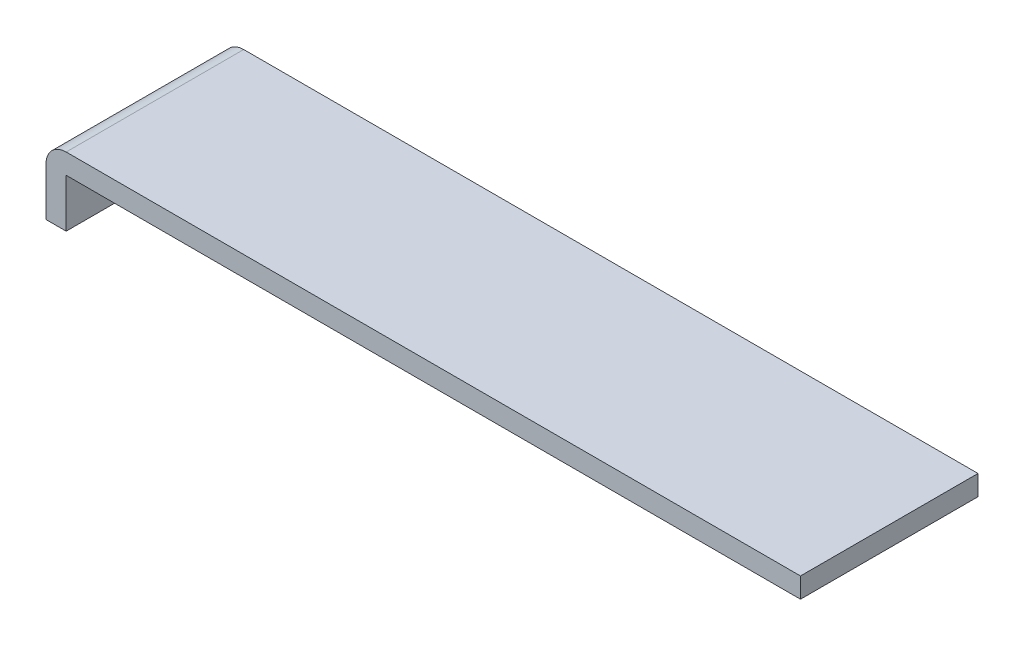
SolidWorks part; units mm, degrees
ref_plane "Plan de face" through (0, 0, 0) normal (0, 0, 1) x (1, 0, 0)
ref_plane "Plan de dessus" through (0, 0, 0) normal (0, 1, 0) x (1, 0, 0)
ref_plane "Plan de droite" through (0, 0, 0) normal (1, 0, 0) x (0, 0, -1)
sketch "Esquisse1" plane through (0, 0, 0) normal (0, 0, 1) x (1, 0, 0)
  line L0 (0, 0) -> (0, 1.7)
  line L1 (0, 1.7) -> (18.7, 1.7)
  line L2 (18.7, 1.7) -> (18.7, 1.2)
  line L3 (18.7, 1.2) -> (0.5, 1.2)
  line L4 (0.5, 1.2) -> (0.5, 0)
  line L5 (0.5, 0) -> (0, 0)
  dimension "D1" = 18.7
  dimension "D2" = 0.5
  dimension "D3" = 0.5
  dimension "D4" = 1.7
extrude "Boss.-Extru.1" add sketch "Esquisse1" along normal blind 4.4
fillet "Congé1" radius 0.5 1 edges at (0, 1.7, 2.2)
